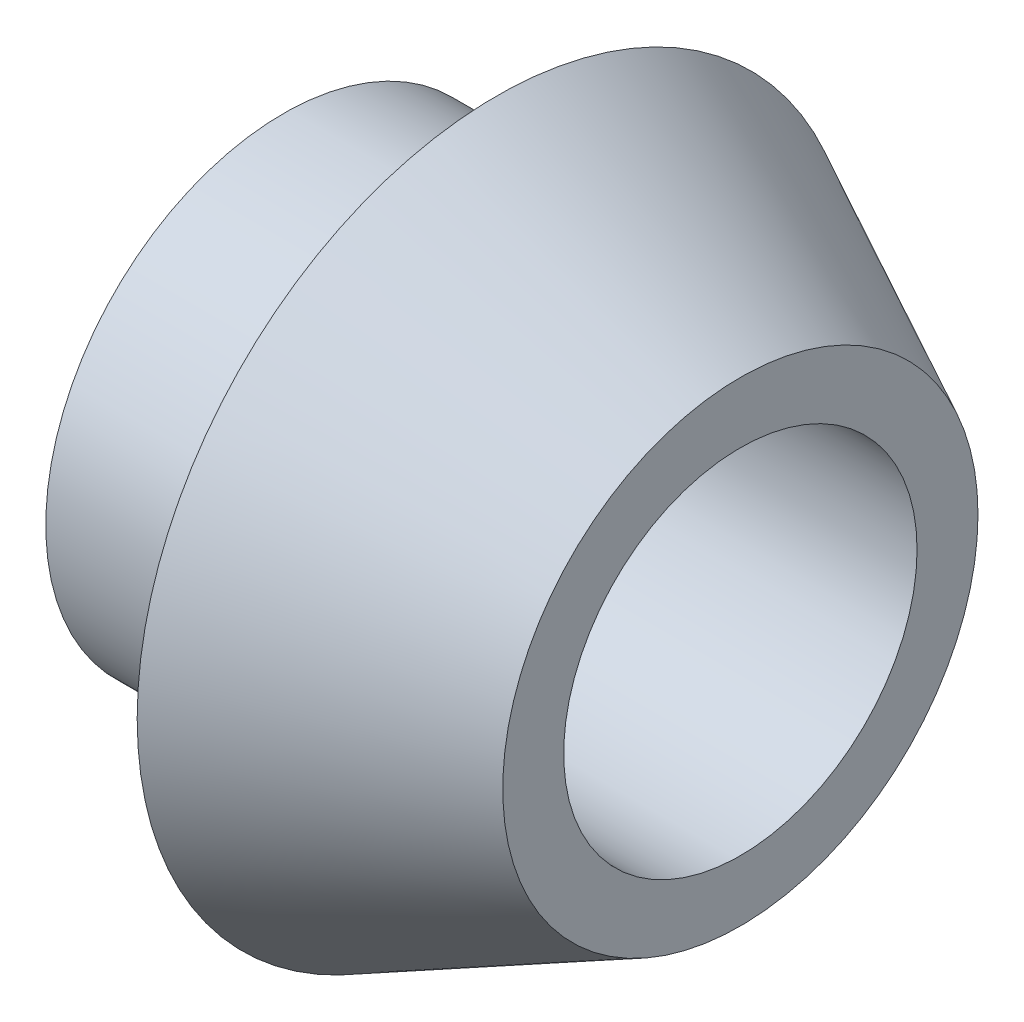
SolidWorks part; units mm, degrees
ref_plane "Front Plane" through (0, 0, 0) normal (0, 0, 1) x (1, 0, 0)
ref_plane "Top Plane" through (0, 0, 0) normal (0, 1, 0) x (1, 0, 0)
ref_plane "Right Plane" through (0, 0, 0) normal (1, 0, 0) x (0, 0, -1)
sketch "Sketch1" plane through (0, 0, 0) normal (0, 0, 1) x (1, 0, 0)
  line L0 (0, 0) -> (7.5, 0)
  line L1 (7.5, 0) -> (7.5, 1)
  line L2 (0, 1) -> (3.5, 1)
  line L3 (3.5, 1) -> (3.5, 3)
  line L4 (0, 1) -> (0, 0)
  line L5 (7.5, -2.9) -> (0, -2.9) construction
  line L6 (3.5, 3) -> (7.5, 1)
  dimension "D1" = 7.5
  dimension "D2" = 3.5
  dimension "D3" = 2
  dimension "D4" = 1
  dimension "D5" = 2.9
  dimension "D6" = 1
revolve "Revolve2" add sketch "Sketch1" angle 360 about L5
